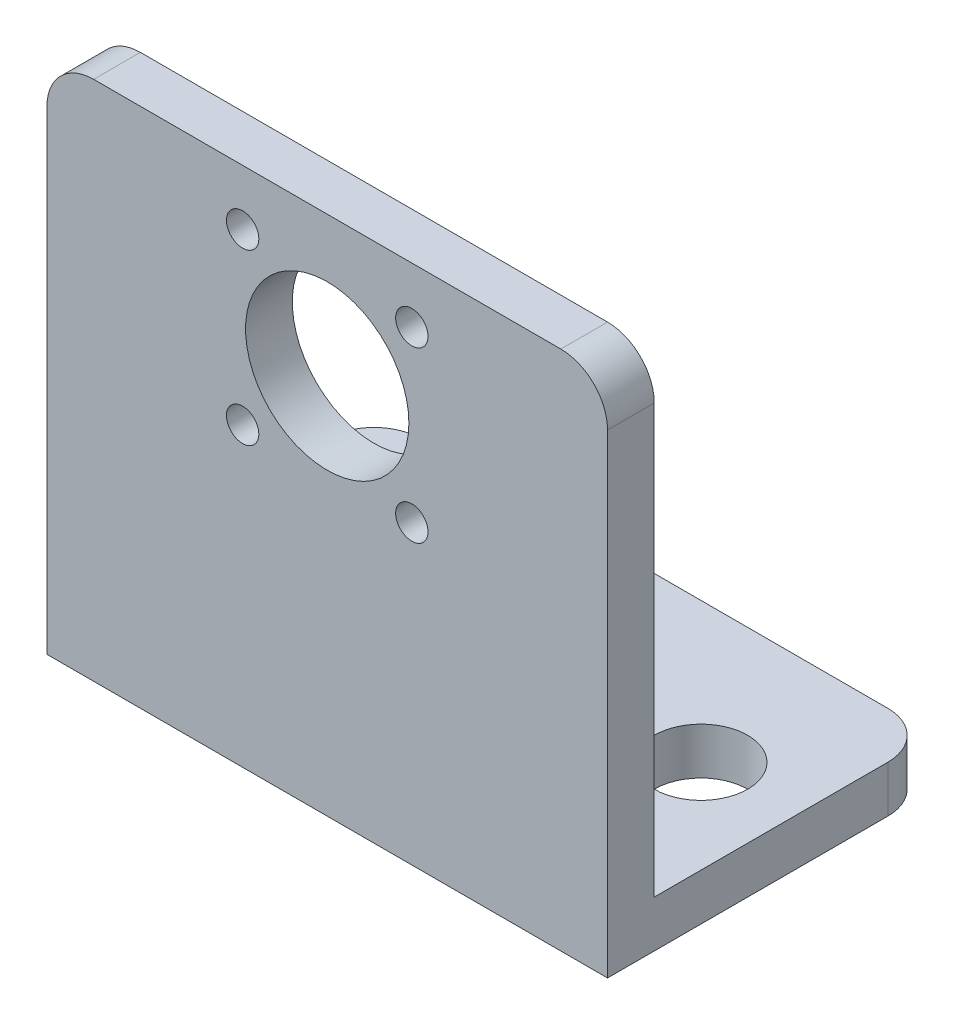
SolidWorks part; units mm, degrees
material "6061-T6 (SS)"
ref_plane "Front Plane" through (0, 0, 0) normal (0, 0, 1) x (1, 0, 0)
ref_plane "Top Plane" through (0, 0, 0) normal (0, 1, 0) x (1, 0, 0)
ref_plane "Right Plane" through (0, 0, 0) normal (1, 0, 0) x (0, 0, -1)
sketch "Sketch1" plane through (0, 0, 0) normal (0, 0, 1) x (1, 0, 0)
  line L0 (-19.05, -25.908) -> (19.05, -25.908)
  line L1 (-19.05, 9.525) -> (19.05, 9.525)
  line L2 (0, 0) -> (0, -25.908) construction
  line L3 (-19.05, 9.525) -> (-19.05, -25.908)
  line L4 (19.05, 9.525) -> (19.05, -25.908)
  circle A0 centre (0, 0) radius 5.55
  dimension "D2" = 11.1
  dimension "D3" = 9.525
  dimension "D1" = 25.908
  dimension "D5" = 38.1
extrude "Boss-Extrude1" add sketch "Sketch1" along normal blind 3.175
sketch "Sketch3" plane through (0, 0, 0) normal (0, 0, -1) x (-1, 0, 0)
  line L0 (-19.05, -25.908) -> (-19.05, 9.525) construction
  line L1 (19.05, -25.908) -> (-19.05, -25.908)
  line L2 (19.05, -25.908) -> (19.05, -22.733)
  line L3 (19.05, -22.733) -> (-19.05, -22.733)
  line L4 (-19.05, -25.908) -> (-19.05, -22.733)
  dimension "D1" = 3.175
extrude "Boss-Extrude2" add sketch "Sketch3" along normal blind 19.05
fillet "Fillet1" radius 3.175 4 edges at (-19.05, 9.525, 1.5875) (19.05, 9.525, 1.5875) (19.05, -24.3205, -19.05) (-19.05, -24.3205, -19.05)
hole_wizard "M2 Clearance Hole1" positions "Sketch7" profile "Sketch8" hole size "M2" standard "ANSI Metric" end condition through all
sketch "Sketch7" plane through (0, -25.908, 3.175) normal (0, 0, 1) x (1, 0, 0)
  point P0 (5.75, 31.658)
  point P2 (-5.75, 31.658)
  point P4 (5.75, 20.158)
  point P6 (-5.75, 20.158)
sketch "Sketch8" plane through (5.75, 5.75, 3.175) normal (1, 0, 0) x (0, -1, 0)
  line L0 (0, 0) -> (0, 22.225)
  line L1 (0, 22.225) -> (1.1, 22.225)
  line L2 (1.1, 22.225) -> (1.1, 0)
  line L3 (1.1, 0) -> (0, 0)
  line L4 (0, -6.35) -> (0, 107.95) construction
  dimension "Thru Hole Dia." = 2.2
  dimension "Thru Hole Depth" = 22.225
hole_wizard "1/4 (0.25) Diameter Hole1" positions "Sketch9" profile "Sketch10" hole size "1/4" standard "ANSI Inch" end condition through all
sketch "Sketch9" plane through (0, -22.733, 0) normal (0, 1, 0) x (1, 0, 0)
  line L0 (-12.7, 9.525) -> (0, 0) construction
  line L1 (-19.05, 0) -> (19.05, 0) construction
  line L2 (0, 0) -> (12.7, 9.525) construction
  point P0 (-12.7, 9.525)
  point P2 (12.7, 9.525)
  point P12 (0, 0)
  dimension "D1" = 25.4
  dimension "D2" = 9.525
sketch "Sketch10" plane through (-12.7, -22.733, -9.525) normal (1, 0, 0) x (0, 0, 1)
  line L0 (0, 0) -> (0, 3.175)
  line L1 (0, 3.175) -> (3.175, 3.175)
  line L2 (3.175, 3.175) -> (3.175, 0)
  line L5 (3.175, 0) -> (0, 0)
  line L11 (0, -6.35) -> (0, 107.95) construction
  dimension "Thru Hole Dia." = 6.35
  dimension "Thru Hole Depth" = 3.175
